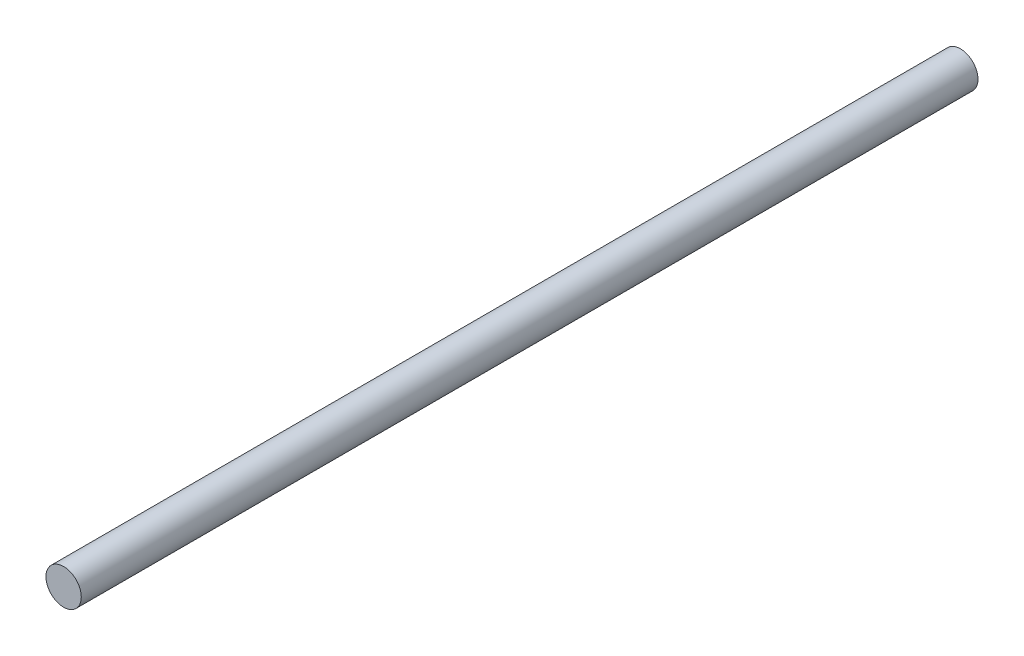
SolidWorks part; units mm, degrees
material "Alloy Steel"
ref_plane "Front Plane" through (0, 0, 0) normal (0, 0, 1) x (1, 0, 0)
ref_plane "Top Plane" through (0, 0, 0) normal (0, 1, 0) x (1, 0, 0)
ref_plane "Right Plane" through (0, 0, 0) normal (1, 0, 0) x (0, 0, -1)
sketch "Sketch1" plane through (0, 0, 0) normal (0, 0, 1) x (1, 0, 0)
  circle A0 centre (0, 0) radius 3
  dimension "D1" = 6
extrude "Boss-Extrude1" add sketch "Sketch1" along normal blind 152.4
equation "\"width\" = 6in 'side to side 6"
equation "\"height\"= 1.25in'top to bottom from 1.25"
equation "\"length\"=6.25in 'back to front 6.25"
equation "\"deapth\"=5in '"
equation "\"side_width\"= 1in"
equation "\"wheel_di\"=1.875in'2.375"
equation "\"wepon_di\" = 1.25in ' milled rectangle must compensate for bolts ~ - .5 1.5"
equation "\"wepon_axle\" = 0.1in ' placement from front .5"
equation "\"D1@Boss-Extrude1\"=\"width\""
equation "\"frame_bolts\" = 0.125"
equation "\"wheel_base\"= 2.5in"
